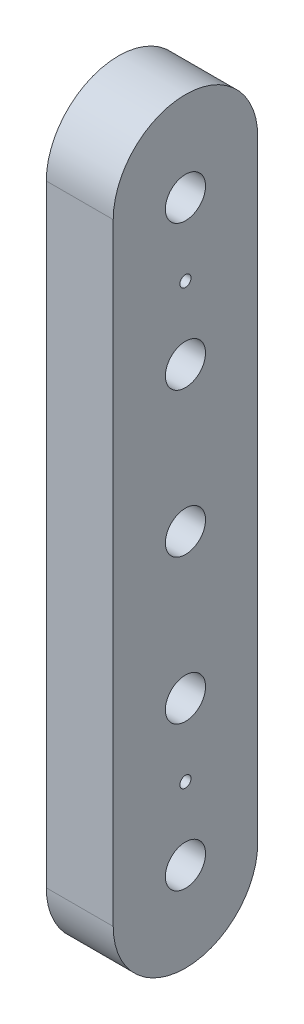
SolidWorks part; units mm, degrees
material "201 Annealed Stainless Steel (SS)"
ref_plane "Front Plane" through (0, 0, 0) normal (0, 0, 1) x (1, 0, 0)
ref_plane "Top Plane" through (0, 0, 0) normal (0, 1, 0) x (1, 0, 0)
ref_plane "Right Plane" through (0, 0, 0) normal (1, 0, 0) x (0, 0, -1)
sketch "Sketch2" plane through (1066.3468, 0, 0) normal (-1, 0, 0) x (0, 0, 1)
  line L4 (-82.55, 1331.1638) -> (-82.55, 2028.051)
  line L5 (-247.0496, 2028.051) -> (-247.0496, 1331.1638)
  line L6 (-82.55, 1331.1638) -> (-82.55, 2028.051)
  line L7 (-247.0496, 2028.051) -> (-247.0496, 1331.1638)
  arc A4 (-82.55, 2028.051) -> (-247.0496, 2028.051) centre (-164.7998, 2028.051) ccw
  arc A5 (-247.0496, 1331.1638) -> (-82.55, 1331.1638) centre (-164.7998, 1331.1638) ccw
  arc A6 (-82.55, 2028.051) -> (-247.0496, 2028.051) centre (-164.7998, 2028.051) ccw
  arc A7 (-247.0496, 1331.1638) -> (-82.55, 1331.1638) centre (-164.7998, 1331.1638) ccw
  dimension "D1" = 25.4
extrude "Boss-Extrude1" add sketch "Sketch2" along normal up to vertex (76.2 mm away)
sketch "Sketch3" plane through (1066.3468, 0, 0) normal (1, 0, 0) x (0, 0, -1)
  circle A20 centre (164.7998, 1844.1541) radius 22.86
  circle A21 centre (164.7998, 1679.6074) radius 22.86
  circle A22 centre (164.7998, 1679.6074) radius 22.86
  circle A23 centre (164.7998, 2008.7008) radius 22.86
  circle A24 centre (164.7998, 1515.0607) radius 22.86
  circle A25 centre (164.7998, 1350.514) radius 22.86
  dimension "D1" = 21.59
extrude "Cut-Extrude1" cut sketch "Sketch3" against normal up to next
sketch "Sketch4" plane through (1066.3468, 0, 0) normal (1, 0, 0) x (0, 0, -1)
  circle A0 centre (164.7998, 1926.4275) radius 6.35 construction
  circle A1 centre (164.7998, 1432.7873) radius 6.35 construction
  circle A2 centre (164.7998, 1926.4275) radius 6.35
  circle A3 centre (164.7998, 1432.7873) radius 6.35
extrude "Cut-Extrude2" cut sketch "Sketch4" against normal up to next
